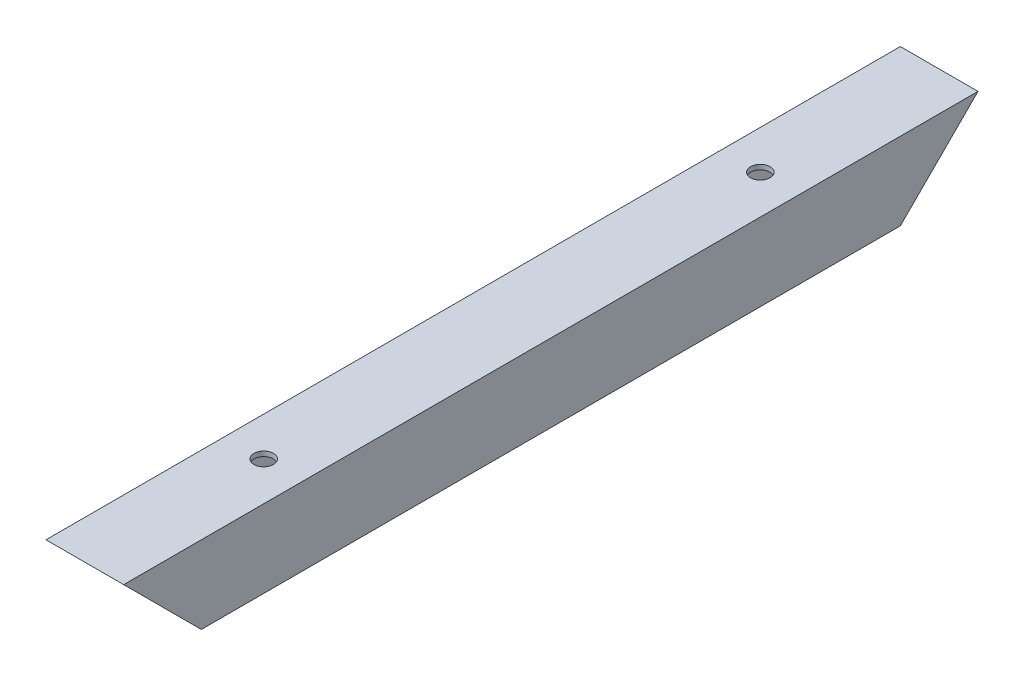
SolidWorks part; units mm, degrees
ref_plane "Front Plane" through (0, 0, 0) normal (0, 0, 1) x (1, 0, 0)
ref_plane "Top Plane" through (0, 0, 0) normal (0, 1, 0) x (1, 0, 0)
ref_plane "Right Plane" through (0, 0, 0) normal (1, 0, 0) x (0, 0, -1)
sketch "Sketch1" plane through (0, 0, 91.6) normal (0, 0, 1) x (1, 0, 0)
  line L1 (488.95, 1117.6) -> (539.75, 1117.6)
  line L2 (488.95, 1117.6) -> (488.95, 1066.8)
  line L3 (488.95, 1066.8) -> (539.75, 1066.8)
  line L4 (539.75, 1117.6) -> (539.75, 1066.8)
  dimension "D1" = 50.8
extrude "Extrude-Thin1" add sketch "Sketch1" along normal blind 279.4 thin
sketch "Sketch2" plane through (539.75, 0, 0) normal (1, 0, 0) x (0, 0, -1)
  line L0 (-371, 1117.6) -> (-320.2, 1066.8)
  line L1 (-371, 1066.8) -> (-91.6, 1066.8) construction
  line L3 (-371, 1066.8) -> (-320.2, 1066.8) construction
  line L4 (-371, 1066.8) -> (-371, 1117.6) construction
extrude "Cut-Extrude1" cut sketch "Sketch2" against normal through all and the other way through all flip side to cut
sketch "Sketch3" plane through (0, 1117.6, 0) normal (0, 1, 0) x (1, 0, 0)
  line L0 (488.95, -231.3) -> (539.75, -231.3) construction
  line L2 (514.35, -231.3) -> (514.35, -254) construction
  line L6 (488.95, -371) -> (488.95, -91.6) construction
  line L7 (539.75, -371) -> (539.75, -91.6) construction
  circle A0 centre (514.35, -254) radius 6.35
  circle A1 centre (507.8481, 254) radius 6.35
  dimension "D2" = 12.7
extrude "Cut-Extrude2" cut sketch "Sketch3" against normal through all
mirror "Mirror1" about plane through (488.95, 1066.8, 91.6) normal (0, 0, 1) of "Cut-Extrude2", "Cut-Extrude1", "Extrude-Thin1"
